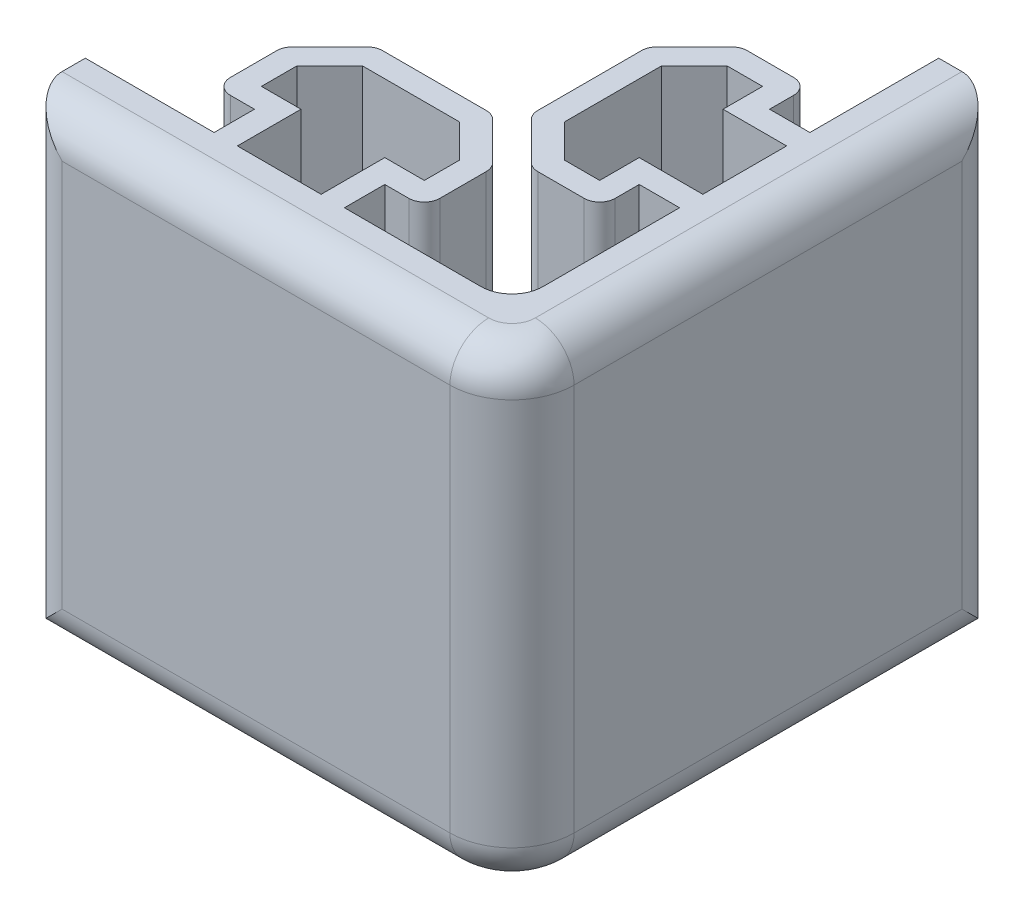
SolidWorks part; units mm, degrees
ref_plane "Front Plane" through (0, 0, 0) normal (0, 0, 1) x (1, 0, 0)
ref_plane "Top Plane" through (0, 0, 0) normal (0, 1, 0) x (1, 0, 0)
ref_plane "Right Plane" through (0, 0, 0) normal (1, 0, 0) x (0, 0, -1)
sketch "Sketch1" plane through (0, 0, 0) normal (0, 1, 0) x (1, 0, 0)
  line L0 (19, 19) -> (19, -19)
  line L1 (15, 15) -> (-15, 15)
  line L2 (15, 15) -> (15, -15)
  line L3 (15, -15) -> (-15, -15)
  line L4 (-15, 15) -> (-15, -15)
  line L5 (15, 15) -> (-15, -15) construction
  line L6 (15, -15) -> (-15, 15) construction
  line L7 (19, -19) -> (-19, -19)
  line L8 (-19, 19) -> (-19, -19)
  line L9 (19, 19) -> (-19, 19)
  line L10 (-15, -15) -> (-15, -19)
  line L11 (15, 15) -> (19, 15)
  line L12 (-15, 0) -> (15, 0) construction
  line L13 (0, 15) -> (0, -15) construction
  line L14 (-6.75, -8) -> (-3.75, -5)
  line L15 (-4.2, -12.4) -> (4.2, -12.4)
  line L16 (-4.2, -12.4) -> (-4.2, -15)
  line L17 (-4.2, -15) -> (4.2, -15)
  line L18 (4.2, -12.4) -> (4.2, -15)
  line L19 (-4.2, -12.4) -> (4.2, -15) construction
  line L20 (-4.2, -15) -> (4.2, -12.4) construction
  line L21 (-6.75, -8) -> (6.75, -8)
  line L22 (-6.75, -8) -> (-6.75, -12.4)
  line L23 (-6.75, -12.4) -> (6.75, -12.4)
  line L24 (6.75, -8) -> (6.75, -12.4)
  line L25 (-6.75, -8) -> (6.75, -12.4) construction
  line L26 (-6.75, -12.4) -> (6.75, -8) construction
  line L27 (-3.75, -5) -> (3.75, -5)
  line L28 (-3.75, -5) -> (-3.75, -8)
  line L29 (-3.75, -8) -> (3.75, -8)
  line L30 (3.75, -5) -> (3.75, -8)
  line L31 (-3.75, -5) -> (3.75, -8) construction
  line L32 (-3.75, -8) -> (3.75, -5) construction
  line L33 (3.75, -5) -> (6.75, -8)
  line L34 (12.4, -4.2) -> (15, -4.2)
  line L35 (12.4, 4.2) -> (15, 4.2)
  line L36 (8, 6.75) -> (5, 3.75)
  line L37 (5, 3.75) -> (5, -3.75)
  line L38 (5, -3.75) -> (8, -6.75)
  line L39 (8, 6.75) -> (12.4, 6.75)
  line L40 (12.4, 6.75) -> (12.4, -6.75)
  line L41 (8, -6.75) -> (12.4, -6.75)
  circle A0 centre (15, -15) radius 4
  point P0 (0, 0)
  point P16 (0, -13.7)
  point P21 (0, -10.2)
  point P26 (0, -6.5)
  dimension "D1" = 30
  dimension "D3" = 8.4
  dimension "D4" = 2.6
  dimension "D5" = 13.5
  dimension "D6" = 4.4
  dimension "D7" = 7.5
  dimension "D8" = 10
  dimension "D2" = 4
extrude "Boss-Extrude1" add sketch "Sketch1" along normal blind 30 contours A0 L3 L10 L7 | A0 L2 L3 | A0 L0 L11 L2 | L35 L40 L34 L2 | L38 L41 L40 L39 L36 L37 | L18 L15 L16 L3 | L24 L21 L22 L23 L15 | L28 L14 L21 | L30 L27 L28 L21 | L33 L30 L21
sketch "Sketch4" plane through (0, 0, 19) normal (0, 0, 1) x (1, 0, 0)
  line L0 (15, 0) -> (-15, 0) construction
  line L1 (-15, 30) -> (-12.5, 30)
  line L2 (-15, 30) -> (-15, 0)
  line L3 (-15, 0) -> (-12.5, 0)
  line L4 (-12.5, 30) -> (-12.5, 0)
  dimension "D1" = 2.5
extrude "Cut-Extrude3" cut sketch "Sketch4" against normal up to next
sketch "Sketch5" plane through (19, 0, 0) normal (1, 0, 0) x (0, 0, -1)
  line L0 (15, 0) -> (-15, 0) construction
  line L1 (15, 30) -> (12.5, 30)
  line L2 (15, 30) -> (15, 0)
  line L3 (15, 0) -> (12.5, 0)
  line L4 (12.5, 30) -> (12.5, 0)
  dimension "D1" = 2.5
extrude "Cut-Extrude4" cut sketch "Sketch5" against normal up to next
fillet "Fillet1" radius 2.5 8 edges at (1.25, 0, 19) (19, 0, 1.25) (1.25, 30, 19) (19, 30, 1.25) (17.8284, 0, 17.8284) (17.8284, 30, 17.8284) (19, 15, -12.5) (-12.5, 15, 19)
fillet "Fillet2" radius 2 1 edges at (15, 15, 15)
fillet "Fillet3" radius 1 12 edges at (12.4, 15, -6.75) (8, 15, -6.75) (5, 15, -3.75) (5, 15, 3.75) (8, 15, 6.75) (12.4, 15, 6.75) (6.75, 15, 12.4) (-6.75, 15, 12.4) (-3.75, 15, 5) (-6.75, 15, 8) (3.75, 15, 5) (6.75, 15, 8)
sketch "Sketch6" plane through (0, 30, 0) normal (0, 1, 0) x (1, 0, 0)
  line L0 (3.1287, -6.5) -> (-3.1287, -6.5)
  line L1 (-3.1287, -6.5) -> (-5.25, -8.6213)
  line L2 (-5.25, -8.6213) -> (-5.25, -10.9)
  line L3 (-5.25, -10.9) -> (-2.7, -10.9)
  line L4 (-2.7, -10.9) -> (-2.7, -15)
  line L5 (-2.7, -15) -> (-2.7, -15)
  line L6 (-2.7, -15) -> (-2.7, -15)
  line L7 (-2.7, -15) -> (15, -15)
  line L8 (15, -15) -> (15, 2.7)
  line L9 (15, 2.7) -> (15, 2.7)
  line L10 (15, 2.7) -> (15, 2.7)
  line L11 (15, 2.7) -> (10.9, 2.7)
  line L12 (10.9, 2.7) -> (10.9, 5.25)
  line L13 (10.9, 5.25) -> (8.6213, 5.25)
  line L14 (8.6213, 5.25) -> (6.5, 3.1287)
  line L15 (6.5, 3.1287) -> (6.5, -3.1287)
  line L16 (6.5, -3.1287) -> (8.6213, -5.25)
  line L17 (8.6213, -5.25) -> (10.9, -5.25)
  line L18 (10.9, -5.25) -> (10.9, -2.7)
  line L19 (10.9, -2.7) -> (16.5, -2.7)
  line L20 (16.5, -2.7) -> (16.5, -13)
  line L21 (13, -16.5) -> (2.7, -16.5)
  line L22 (2.7, -16.5) -> (2.7, -10.9)
  line L23 (2.7, -10.9) -> (5.25, -10.9)
  line L24 (5.25, -10.9) -> (5.25, -8.6213)
  line L25 (5.25, -8.6213) -> (3.1287, -6.5)
  line L26 (12.4, 4.2) -> (12.4, 5.75)
  line L27 (11.4, 6.75) -> (8.4142, 6.75)
  line L28 (7.7071, 6.4571) -> (5.2929, 4.0429)
  line L29 (5, 3.3358) -> (5, -3.3358)
  line L30 (5.2929, -4.0429) -> (7.7071, -6.4571)
  line L31 (8.4142, -6.75) -> (11.4, -6.75)
  line L32 (12.4, -5.75) -> (12.4, -4.2)
  line L33 (12.4, -4.2) -> (15, -4.2)
  line L34 (15, -4.2) -> (15, -13)
  line L35 (13, -15) -> (4.2, -15)
  line L36 (4.2, -15) -> (4.2, -12.4)
  line L37 (4.2, -12.4) -> (5.75, -12.4)
  line L38 (6.75, -11.4) -> (6.75, -8.4142)
  line L39 (6.4571, -7.7071) -> (4.0429, -5.2929)
  line L40 (3.3358, -5) -> (-3.3358, -5)
  line L41 (-4.0429, -5.2929) -> (-6.4571, -7.7071)
  line L42 (-6.75, -8.4142) -> (-6.75, -11.4)
  line L43 (-5.75, -12.4) -> (-4.2, -12.4)
  line L44 (-4.2, -12.4) -> (-4.2, -15)
  line L45 (-4.2, -15) -> (-12.5, -15)
  line L46 (-12.5, -15) -> (-12.5, -16.5)
  line L47 (-12.5, -16.5) -> (15, -16.5)
  line L48 (16.5, -15) -> (16.5, 12.5)
  line L49 (16.5, 12.5) -> (15, 12.5)
  line L50 (15, 12.5) -> (15, 4.2)
  line L51 (15, 4.2) -> (12.4, 4.2)
  line L52 (12.4, 4.2) -> (12.4, 5.75)
  line L53 (11.4, 6.75) -> (8.4142, 6.75)
  line L54 (7.7071, 6.4571) -> (5.2929, 4.0429)
  line L55 (5, 3.3358) -> (5, -3.3358)
  line L56 (5.2929, -4.0429) -> (7.7071, -6.4571)
  line L57 (8.4142, -6.75) -> (11.4, -6.75)
  line L58 (12.4, -5.75) -> (12.4, -4.2)
  line L59 (12.4, -4.2) -> (15, -4.2)
  line L60 (15, -4.2) -> (15, -13)
  line L61 (13, -15) -> (4.2, -15)
  line L62 (4.2, -15) -> (4.2, -12.4)
  line L63 (4.2, -12.4) -> (5.75, -12.4)
  line L64 (6.75, -11.4) -> (6.75, -8.4142)
  line L65 (6.4571, -7.7071) -> (4.0429, -5.2929)
  line L66 (3.3358, -5) -> (-3.3358, -5)
  line L67 (-4.0429, -5.2929) -> (-6.4571, -7.7071)
  line L68 (-6.75, -8.4142) -> (-6.75, -11.4)
  line L69 (-5.75, -12.4) -> (-4.2, -12.4)
  line L70 (-4.2, -12.4) -> (-4.2, -15)
  line L71 (-4.2, -15) -> (-12.5, -15)
  line L72 (-12.5, -15) -> (-12.5, -16.5)
  line L73 (-12.5, -16.5) -> (15, -16.5)
  line L74 (16.5, -15) -> (16.5, 12.5)
  line L75 (16.5, 12.5) -> (15, 12.5)
  line L76 (15, 12.5) -> (15, 4.2)
  line L77 (15, 4.2) -> (12.4, 4.2)
  arc A0 (-3.1287, -6.5) -> (-3.1287, -6.5) centre (-3.1287, -6.5) ccw
  arc A1 (-5.25, -8.6213) -> (-5.25, -8.6213) centre (-5.25, -8.6213) ccw
  arc A2 (-5.25, -10.9) -> (-5.25, -10.9) centre (-5.25, -10.9) ccw
  arc A3 (15, -15) -> (15, -15) centre (15, -15) ccw
  arc A4 (10.9, 5.25) -> (10.9, 5.25) centre (10.9, 5.25) ccw
  arc A5 (8.6213, 5.25) -> (8.6213, 5.25) centre (8.6213, 5.25) ccw
  arc A6 (6.5, 3.1287) -> (6.5, 3.1287) centre (6.5, 3.1287) ccw
  arc A7 (6.5, -3.1287) -> (6.5, -3.1287) centre (6.5, -3.1287) ccw
  arc A8 (8.6213, -5.25) -> (8.6213, -5.25) centre (8.6213, -5.25) ccw
  arc A9 (10.9, -5.25) -> (10.9, -5.25) centre (10.9, -5.25) ccw
  arc A10 (13, -16.5) -> (16.5, -13) centre (13, -13) ccw
  arc A11 (5.25, -10.9) -> (5.25, -10.9) centre (5.25, -10.9) ccw
  arc A12 (5.25, -8.6213) -> (5.25, -8.6213) centre (5.25, -8.6213) ccw
  arc A13 (3.1287, -6.5) -> (3.1287, -6.5) centre (3.1287, -6.5) ccw
  arc A14 (12.4, 5.75) -> (11.4, 6.75) centre (11.4, 5.75) ccw
  arc A15 (8.4142, 6.75) -> (7.7071, 6.4571) centre (8.4142, 5.75) ccw
  arc A16 (5.2929, 4.0429) -> (5, 3.3358) centre (6, 3.3358) ccw
  arc A17 (5, -3.3358) -> (5.2929, -4.0429) centre (6, -3.3358) ccw
  arc A18 (7.7071, -6.4571) -> (8.4142, -6.75) centre (8.4142, -5.75) ccw
  arc A19 (11.4, -6.75) -> (12.4, -5.75) centre (11.4, -5.75) ccw
  arc A20 (13, -15) -> (15, -13) centre (13, -13) ccw
  arc A21 (5.75, -12.4) -> (6.75, -11.4) centre (5.75, -11.4) ccw
  arc A22 (6.75, -8.4142) -> (6.4571, -7.7071) centre (5.75, -8.4142) ccw
  arc A23 (4.0429, -5.2929) -> (3.3358, -5) centre (3.3358, -6) ccw
  arc A24 (-3.3358, -5) -> (-4.0429, -5.2929) centre (-3.3358, -6) ccw
  arc A25 (-6.4571, -7.7071) -> (-6.75, -8.4142) centre (-5.75, -8.4142) ccw
  arc A26 (-6.75, -11.4) -> (-5.75, -12.4) centre (-5.75, -11.4) ccw
  arc A27 (15, -16.5) -> (16.5, -15) centre (15, -15) ccw
  arc A28 (12.4, 5.75) -> (11.4, 6.75) centre (11.4, 5.75) ccw
  arc A29 (8.4142, 6.75) -> (7.7071, 6.4571) centre (8.4142, 5.75) ccw
  arc A30 (5.2929, 4.0429) -> (5, 3.3358) centre (6, 3.3358) ccw
  arc A31 (5, -3.3358) -> (5.2929, -4.0429) centre (6, -3.3358) ccw
  arc A32 (7.7071, -6.4571) -> (8.4142, -6.75) centre (8.4142, -5.75) ccw
  arc A33 (11.4, -6.75) -> (12.4, -5.75) centre (11.4, -5.75) ccw
  arc A34 (13, -15) -> (15, -13) centre (13, -13) ccw
  arc A35 (5.75, -12.4) -> (6.75, -11.4) centre (5.75, -11.4) ccw
  arc A36 (6.75, -8.4142) -> (6.4571, -7.7071) centre (5.75, -8.4142) ccw
  arc A37 (4.0429, -5.2929) -> (3.3358, -5) centre (3.3358, -6) ccw
  arc A38 (-3.3358, -5) -> (-4.0429, -5.2929) centre (-3.3358, -6) ccw
  arc A39 (-6.4571, -7.7071) -> (-6.75, -8.4142) centre (-5.75, -8.4142) ccw
  arc A40 (-6.75, -11.4) -> (-5.75, -12.4) centre (-5.75, -11.4) ccw
  arc A41 (15, -16.5) -> (16.5, -15) centre (15, -15) ccw
  dimension "D1" = 0
  dimension "D2" = 1.5
extrude "Cut-Extrude5" cut sketch "Sketch6" against normal up to next contours L24 L25 L0 L1 L2 L3 L4 L7 L22 L23 | L18 L19 L8 L11 L12 L13 L14 L15 L16 L17
